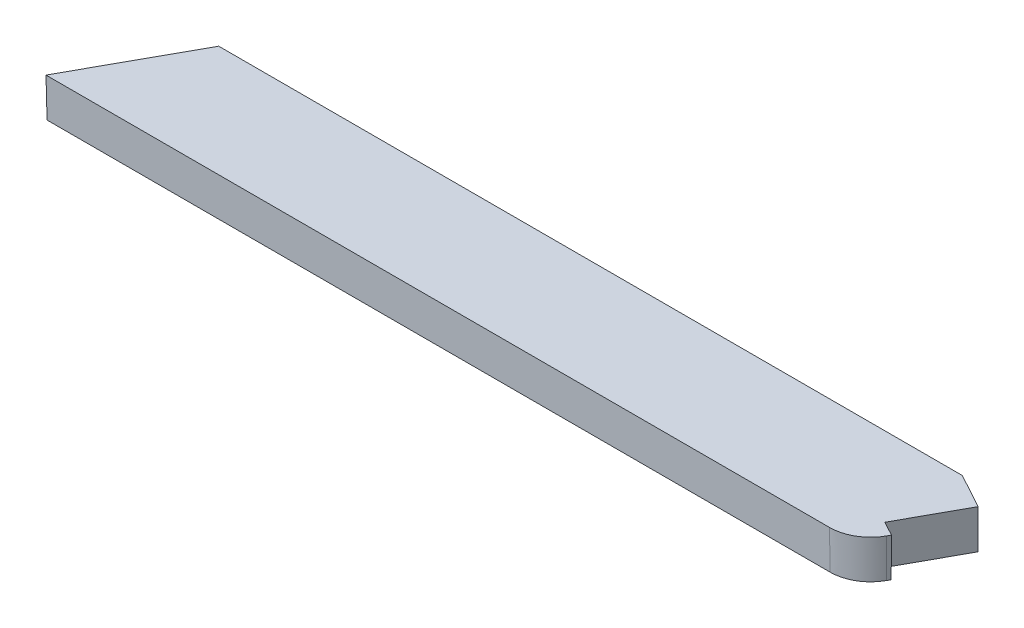
SolidWorks part; units mm, degrees
ref_plane "Front Plane" through (0, 0, 0) normal (0, 0, 1) x (1, 0, 0)
ref_plane "Top Plane" through (0, 0, 0) normal (0, 1, 0) x (1, 0, 0)
ref_plane "Right Plane" through (0, 0, 0) normal (1, 0, 0) x (0, 0, -1)
sketch "Sketch1" plane through (0, 0, 0) normal (0, 1, 0) x (1, 0, 0)
  line L0 (0, 0) -> (7.836, 14.23)
  line L1 (7.836, 14.23) -> (111.0358, 14.23)
  line L2 (111.0358, 14.23) -> (103.1999, 0)
  line L3 (103.1999, 0) -> (0, 0)
  dimension "D1" = 61.16
  dimension "D2" = 14.23
  dimension "D3" = 90.4
extrude "Boss-Extrude1" add sketch "Sketch1" along normal blind 5
sketch "Sketch2" plane through (0, 5, 0) normal (0, 1, 0) x (1, 0, 0)
  line L0 (104.9098, 3.1052) -> (103.0702, 4.1181)
  line L1 (103.1999, 0) -> (111.0358, 14.23) construction
  line L2 (108.6385, 14.23) -> (103.0702, 4.1181)
  line L4 (104.9098, 3.1052) -> (111.0358, 14.23)
  line L5 (111.0358, 14.23) -> (7.836, 14.23) construction
  line L6 (111.0358, 14.23) -> (108.6385, 14.23)
  dimension "D1" = 2.1
  dimension "D2" = 12.7
extrude "Cut-Extrude1" cut sketch "Sketch2" against normal up to next
sketch "Sketch4" plane through (0, 5, 0) normal (0, 1, 0) x (1, 0, 0)
  line L0 (108.6385, 14.23) -> (103.0702, 4.1181) construction
  line L1 (108.6385, 14.23) -> (7.836, 14.23) construction
  line L2 (108.6385, 14.23) -> (107.2909, 11.7829)
  line L3 (108.6385, 14.23) -> (102.847, 14.23)
  line L4 (107.2909, 11.7829) -> (102.847, 14.23)
  line L5 (103.0702, 4.1181) -> (104.9098, 3.1052) construction
  dimension "D1" = 8.75
extrude "Cut-Extrude2" cut sketch "Sketch4" against normal up to next
fillet "Fillet1" radius 5.25 1 edges at (103.1999, 2.5, 0)
draft "Draft1" type of draft neutral plane draft angle 1 faces to draft 3 face at (50.0487, 2.5, 0) face at (104.8031, 2.5, -2.9114) face at (102.5827, 2.5, -1.0445) neutral plane through (0, 5, 0) neutral plane normal (0, 1, 0) reverse direction yes parameters "D1"=1
